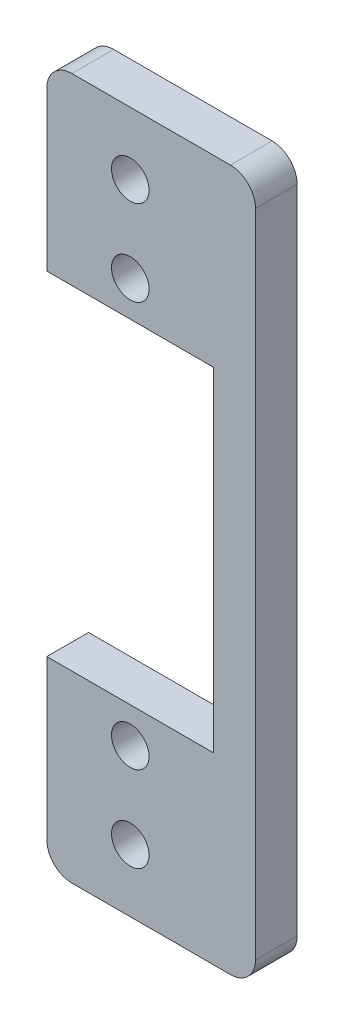
SolidWorks part; units mm, degrees
ref_plane "Front Plane" through (0, 0, 0) normal (0, 0, 1) x (1, 0, 0)
ref_plane "Top Plane" through (0, 0, 0) normal (0, 1, 0) x (1, 0, 0)
ref_plane "Right Plane" through (0, 0, 0) normal (1, 0, 0) x (0, 0, -1)
sketch "Sketch2" plane through (0, 0, 0) normal (0, 0, 1) x (1, 0, 0)
  line L0 (-15, 42) -> (-15, 15) construction
  line L1 (-15, 42) -> (15, 42)
  line L2 (-15, 15) -> (-10, 15) construction
  line L3 (-15, -42) -> (15, -42)
  line L4 (15, 42) -> (15, -42)
  line L5 (-10, 20) -> (10, 20)
  line L6 (-10, 15) -> (-10, 20) construction
  line L7 (-10, -20) -> (10, -20)
  line L8 (10, 20) -> (10, -20)
  line L9 (-10, -20) -> (-10, -15) construction
  line L10 (-10, -15) -> (-15, -15) construction
  line L11 (-15, -15) -> (-15, -42) construction
  line L12 (0, -34.5) -> (0, -42) construction
  line L13 (0, 34.5) -> (0, 42) construction
  line L14 (10, 0) -> (15, 0) construction
  line L15 (0, 24.25) -> (0, -24.25) construction
  line L16 (-10, -20) -> (-10, -42)
  line L17 (-10, 20) -> (-10, 42)
  point P12 (10, 0)
  point P13 (0, 20)
  point P15 (0, -34.5)
  point P16 (0, 34.5)
  point P17 (0, -10)
  point P18 (0, -20)
  point P25 (0, 24.25)
  point P26 (0, -24.25)
  dimension "D1" = 20
  dimension "D2" = 40
  dimension "D3" = 69
  dimension "D4" = 10
  dimension "D5" = 24.5
  dimension "D6" = 7.5
  dimension "D7" = 5
  dimension "D8" = 5
  dimension "D9" = 48.5
extrude "Boss-Extrude1" add sketch "Sketch2" along normal blind 5 contours L17 L5 L8 L7 L16 L3 L4 L1
hole_wizard "M4 Clearance Hole1" positions "Sketch4" profile "Sketch3" hole size "M4" standard "ANSI Metric" end condition through all
sketch "Sketch4" plane through (0, 0, 0) normal (0, 0, 1) x (1, 0, 0)
  point P1 (0, 34.5)
  point P3 (0, -34.5)
sketch "Sketch3" plane through (0, 34.5, 0) normal (1, 0, 0) x (0, 1, 0)
  line L0 (0, 0) -> (0, 5)
  line L1 (0, 5) -> (2.25, 5)
  line L2 (2.25, 5) -> (2.25, 0)
  line L5 (2.25, 0) -> (0, 0)
  line L11 (0, -6.35) -> (0, 107.95) construction
  dimension "Thru Hole Dia." = 4.5
  dimension "Thru Hole Depth" = 5
fillet "Fillet1" radius 3 4 edges at (15, 42, 2.5) (15, -42, 2.5) (-10, 42, 2.5) (-10, -42, 2.5)
hole_wizard "M4 Clearance Hole2" positions "Sketch6" profile "Sketch5" hole size "M4" standard "ANSI Metric" end condition through all
sketch "Sketch6" plane through (0, 0, 0) normal (0, 0, 1) x (1, 0, 0)
  point P1 (0, 24.25)
  point P3 (0, -24.25)
sketch "Sketch5" plane through (0, 24.25, 0) normal (1, 0, 0) x (0, 1, 0)
  line L0 (0, 0) -> (0, 5)
  line L1 (0, 5) -> (2.25, 5)
  line L2 (2.25, 5) -> (2.25, 0)
  line L5 (2.25, 0) -> (0, 0)
  line L11 (0, -6.35) -> (0, 107.95) construction
  dimension "Thru Hole Dia." = 4.5
  dimension "Thru Hole Depth" = 5
equation "\"d_slots\" = 69mm"
equation "\"w_servo\" = 20mm"
equation "\"l_servo\" = 40mm"
equation "\"D1@Sketch2\"=\"w_servo\""
equation "\"D2@Sketch2\"=\"l_servo\""
equation "\"D3@Sketch2\"=\"d_slots\""
equation "\"D4@Sketch2\"=\"d_servocenter\""
equation "\"d_servocenter\"= 10mm"
equation "\"d_centertoslot\" = 24.5mm"
equation "\"D5@Sketch2\"=\"d_centertoslot\""
